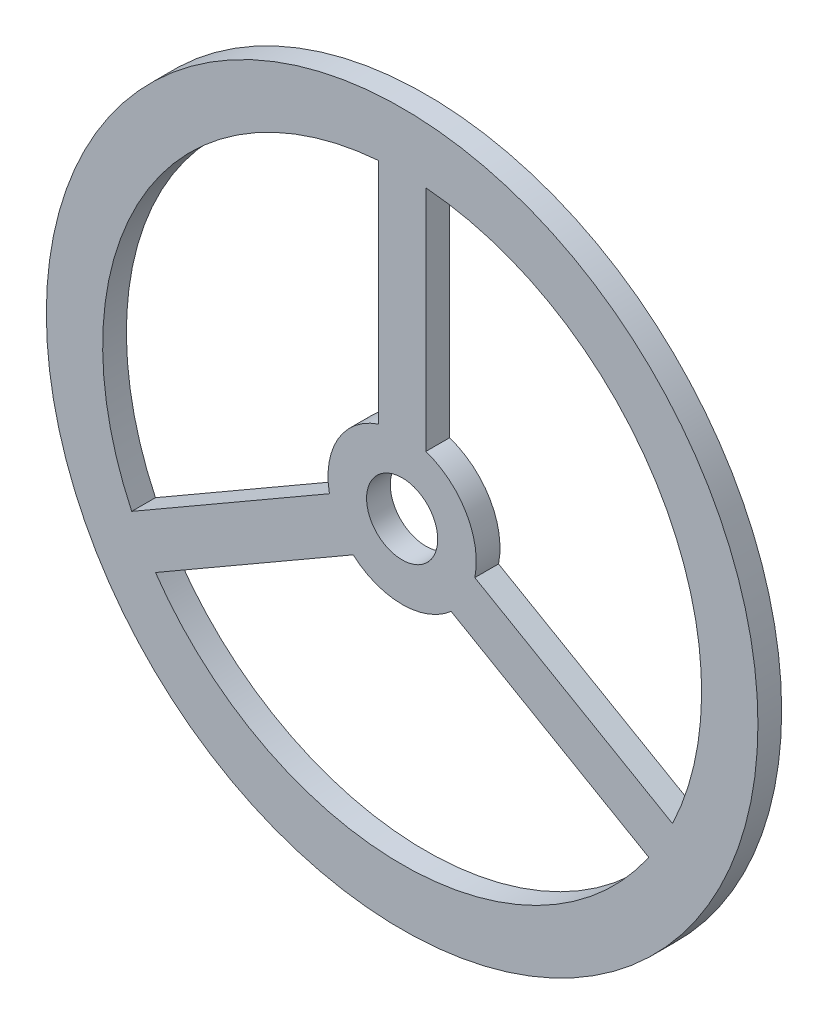
SolidWorks part; units mm, degrees
material "3003 合金"
ref_plane "前视基准面" through (0, 0, 0) normal (0, 0, 1) x (1, 0, 0)
ref_plane "上视基准面" through (0, 0, 0) normal (0, 1, 0) x (1, 0, 0)
ref_plane "右视基准面" through (0, 0, 0) normal (1, 0, 0) x (0, 0, -1)
sketch "草图1" plane through (0, 0, 0) normal (0, 0, 1) x (1, 0, 0)
  line L0 (-4, 11.8427) -> (-4, 50.3413)
  line L1 (0, 0) -> (0, 49.7006) construction
  line L2 (4, 11.8427) -> (4, 50.3413)
  line L3 (12.2561, -2.4573) -> (45.5969, -21.7066)
  line L4 (8.2561, -9.3855) -> (41.5969, -28.6348)
  line L5 (-8.2561, -9.3855) -> (-41.5969, -28.6348)
  line L6 (-12.2561, -2.4573) -> (-45.5969, -21.7066)
  circle A0 centre (0, 0) radius 60
  circle A1 centre (0, 0) radius 6
  arc A2 (-4, 50.3413) -> (-45.5969, -21.7066) centre (0, 0) ccw
  arc A3 (-4, 11.8427) -> (-12.2561, -2.4573) centre (0, 0) ccw
  arc A4 (-41.5969, -28.6348) -> (41.5969, -28.6348) centre (0, 0) ccw
  arc A5 (45.5969, -21.7066) -> (4, 50.3413) centre (0, 0) ccw
  arc A6 (12.2561, -2.4573) -> (4, 11.8427) centre (0, 0) ccw
  arc A7 (-8.2561, -9.3855) -> (8.2561, -9.3855) centre (0, 0) ccw
  dimension "D1" = 120
  dimension "D2" = 25
  dimension "D3" = 101
  dimension "D7" = 12
  dimension "D4" = 4
  dimension "D5" = 4
  dimension "D6" = 3
extrude "凸台-拉伸1" add sketch "草图1" along normal blind 4
